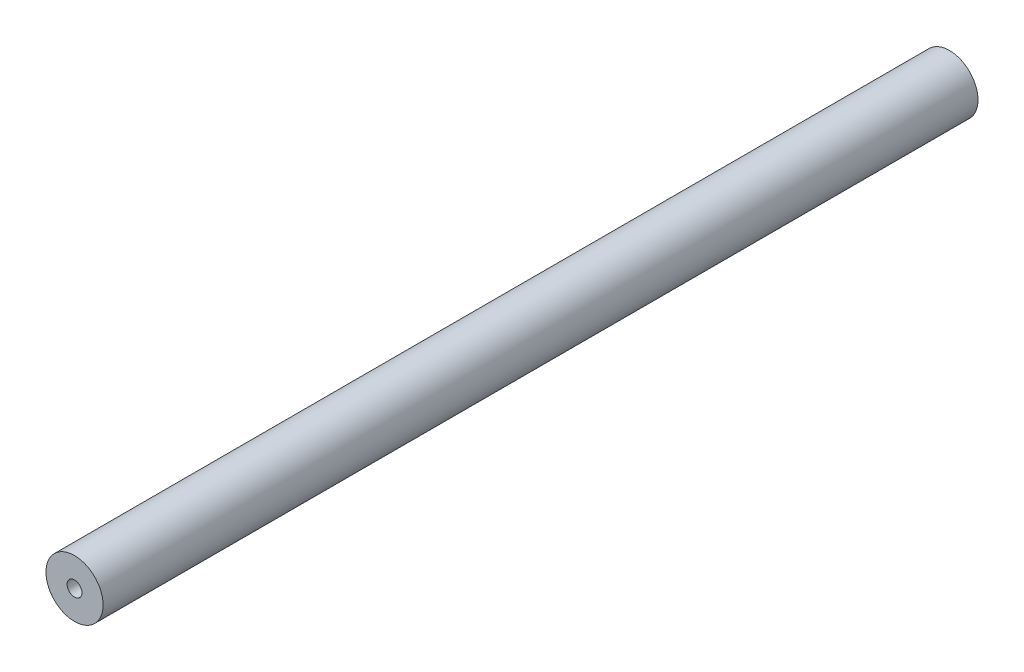
SolidWorks part; units mm, degrees
material "Pine"
ref_plane "Front Plane" through (0, 0, 0) normal (0, 0, 1) x (1, 0, 0)
ref_plane "Top Plane" through (0, 0, 0) normal (0, 1, 0) x (1, 0, 0)
ref_plane "Right Plane" through (0, 0, 0) normal (1, 0, 0) x (0, 0, -1)
sketch "Sketch1" plane through (0, 0, 0) normal (0, 0, 1) x (1, 0, 0)
  circle A0 centre (0, 0) radius 3.9688
  circle A1 centre (0, 0) radius 15.24
  dimension "D1" = 7.9375
  dimension "D2" = 30.48
extrude "Boss-Extrude1" add sketch "Sketch1" along normal mid plane 466.725 contours A0 | A1
